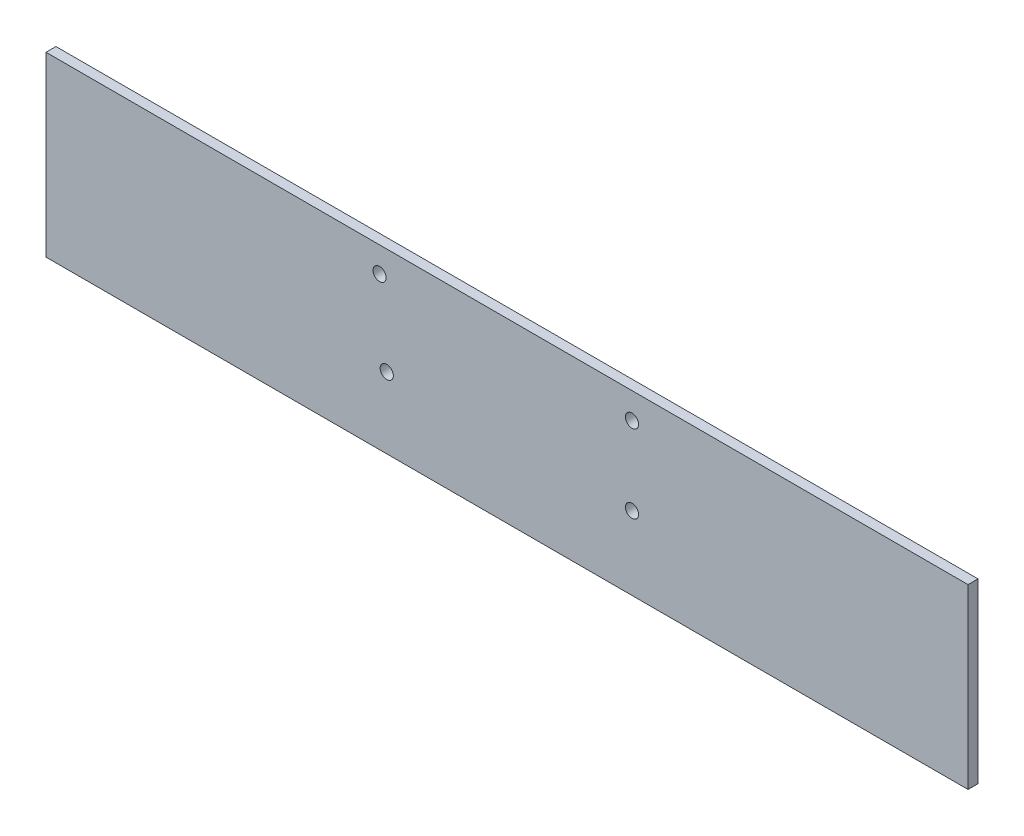
SolidWorks part; units mm, degrees
material "ABS"
ref_plane "X-Y Datum" through (0, 0, 0) normal (0, 0, 1) x (1, 0, 0)
ref_plane "X-Z Datum" through (0, 0, 0) normal (0, 1, 0) x (1, 0, 0)
ref_plane "Y-Z Datum" through (0, 0, 0) normal (1, 0, 0) x (0, 0, -1)
sketch "Sketch1" plane through (0, 0, 0) normal (0, 0, 1) x (1, 0, 0)
  line L1 (10.4879, 139.51) -> (304.6181, 139.51)
  line L2 (10.4879, 139.51) -> (10.4879, 82.9112)
  line L3 (10.4879, 82.9112) -> (304.6181, 82.9112)
  line L4 (304.6181, 139.51) -> (304.6181, 82.9112)
extrude "Boss-Extrude1" add sketch "Sketch1" along normal blind 3.175 contours L1 L4 L3 L2
sketch "Sketch2" plane through (0, 0, 3.175) normal (0, 0, 1) x (1, 0, 0)
  line L0 (195.3175, 131.202) -> (199.5175, 131.202) construction
  line L1 (114.7995, 131.456) -> (118.9995, 131.456) construction
  line L2 (117.0855, 105.548) -> (121.2855, 105.548) construction
  line L3 (195.3175, 106.31) -> (199.5175, 106.31) construction
  line L4 (157.553, 82.9112) -> (157.553, 94.8595) construction
  circle A0 centre (197.4175, 131.202) radius 2.1
  circle A1 centre (116.8995, 131.456) radius 2.1
  circle A2 centre (119.1855, 105.548) radius 2.1
  circle A3 centre (197.4175, 106.31) radius 2.1
extrude "Cut-Extrude1" cut sketch "Sketch2" against normal through all
